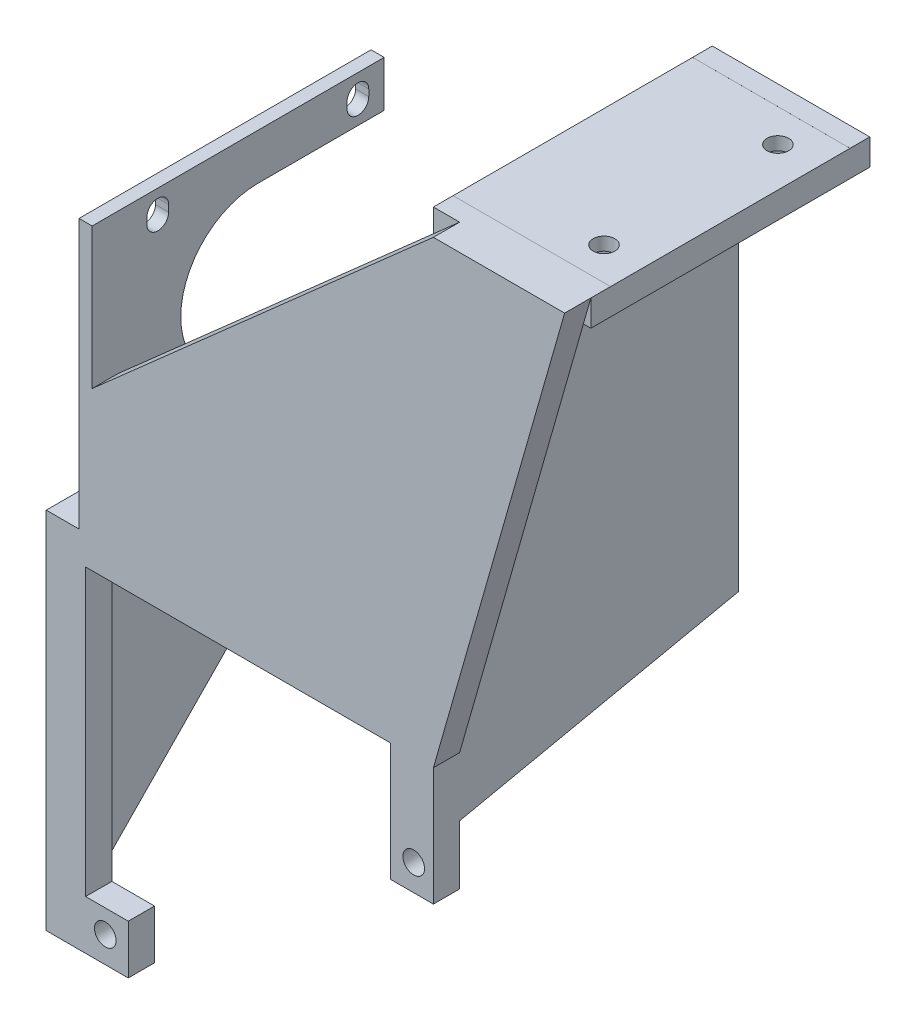
SolidWorks part; units mm, degrees
ref_plane "Front Plane" through (0, 0, 0) normal (0, 0, 1) x (1, 0, 0)
ref_plane "Top Plane" through (0, 0, 0) normal (0, 1, 0) x (1, 0, 0)
ref_plane "Right Plane" through (0, 0, 0) normal (1, 0, 0) x (0, 0, -1)
sketch "Sketch1" plane through (0, 0, 0) normal (1, 0, 0) x (0, 0, -1)
  line L1 (0, 0) -> (13, 0)
  line L2 (0, 0) -> (0, -16)
  line L3 (0, -16) -> (13, -16)
  line L4 (13, 0) -> (13, -16)
  dimension "D1" = 13
  dimension "D2" = 16
extrude "Boss-Extrude1" add sketch "Sketch1" along normal blind 4
sketch "Sketch2" plane through (4, 0, 0) normal (1, 0, 0) x (0, 0, -1)
  line L0 (13, 0) -> (0, 0) construction
  line L1 (0, -16) -> (13, -16) construction
  line L2 (13, -16) -> (13, 0) construction
  line L3 (0, 0) -> (0, -16) construction
  circle A0 centre (6.5, -4) radius 1.65
  circle A1 centre (6.5, -12) radius 1.65
  dimension "D1" = 3.3
  dimension "D2" = 3.3
  dimension "D3" = 4
  dimension "D4" = 4
  dimension "D5" = 6.5
  dimension "D6" = 6.5
extrude "Cut-Extrude1" cut sketch "Sketch2" against normal blind 10
sketch "Sketch3" plane through (0, -16, 0) normal (0, -1, 0) x (1, 0, 0)
  line L1 (4, 0) -> (0, 0)
  line L2 (4, 0) -> (4, -13)
  line L3 (4, -13) -> (0, -13)
  line L4 (0, 0) -> (0, -13)
extrude "Boss-Extrude2" add sketch "Sketch3" along normal blind 4
sketch "Sketch4" plane through (4, 0, 0) normal (1, 0, 0) x (0, 0, -1)
  line L0 (13, -20) -> (13, 0) construction
  line L1 (0, -20) -> (13, -20)
  line L2 (0, -20) -> (0, -16)
  line L3 (0, -16) -> (13, -16)
  line L4 (13, -20) -> (13, -16)
  dimension "D1" = 4
extrude "Boss-Extrude3" add sketch "Sketch4" along normal blind 60
sketch "Sketch6" plane through (0, -16, 0) normal (0, 1, 0) x (1, 0, 0)
  line L0 (64, 0) -> (4, 0) construction
  line L1 (64, 13) -> (60, 13)
  line L2 (64, 13) -> (64, -21)
  line L3 (64, -21) -> (60, -21)
  line L4 (60, 13) -> (60, -21)
  line L7 (64, 13) -> (60, 13)
  line L8 (64, 13) -> (64, 34)
  line L9 (64, 34) -> (60, 34)
  line L10 (60, 13) -> (60, 34)
  line M2 (4, 0) -> (64, 0)
  line M3 (64, 0) -> (64, 13)
  line M4 (64, 13) -> (4, 13)
  dimension "D1" = 4
  dimension "D2" = 21
  dimension "D3" = 21
extrude "Boss-Extrude4" add sketch "Sketch6" along normal blind 28 contours L4 L3 L2 M2 | L10 L8 L9 M4 | L4 M4 M2 M3
sketch "Sketch12" plane through (0, 0, -34) normal (0, 0, -1) x (-1, 0, 0)
  line L1 (-60, -16) -> (-64, -16)
  line L2 (-60, -16) -> (-60, 12)
  line L3 (-60, 12) -> (-64, 12)
  line L4 (-64, -16) -> (-64, 12)
extrude "Boss-Extrude8" add sketch "Sketch12" along normal blind 1.65
sketch "Sketch13" plane through (0, 0, 21) normal (0, 0, 1) x (1, 0, 0)
  line L1 (60, 12) -> (64, 12)
  line L2 (60, 12) -> (60, -16)
  line L3 (60, -16) -> (64, -16)
  line L4 (64, 12) -> (64, -16)
extrude "Boss-Extrude9" add sketch "Sketch13" along normal blind 1.65
sketch "Sketch14" plane through (0, 12, 0) normal (0, 1, 0) x (1, 0, 0)
  line L0 (64, 35.65) -> (64, -22.65) construction
  line L1 (64, 24.35) -> (60, 24.35)
  line L2 (64, 24.35) -> (64, -11.5284)
  line L3 (64, -11.5284) -> (60, -11.5284)
  line L4 (60, 24.35) -> (60, -11.5284)
  line L5 (60, 35.65) -> (60, -22.65) construction
  line L6 (64, -22.65) -> (60, -22.65) construction
  line L7 (60, 35.65) -> (64, 35.65) construction
  point P10 (62, -22.65)
  dimension "D1" = 11.3
  dimension "D2" = 11.3
extrude "Cut-Extrude5" cut sketch "Sketch14" against normal blind 24
sketch "Sketch15" plane through (64, 0, 0) normal (1, 0, 0) x (0, 0, -1)
  line L0 (-11.5284, 12) -> (-22.65, 12) construction
  line L1 (35.65, 12) -> (24.35, 12) construction
  line L2 (-22.65, -16) -> (-22.65, 12) construction
  line L3 (35.65, 12) -> (35.65, -16) construction
  circle A0 centre (-17, -11.5) radius 1.65
  circle A1 centre (30, -11.5) radius 1.65
  dimension "D1" = 3.3
  dimension "D2" = 3.3
  dimension "D3" = 23.5
  dimension "D4" = 23.5
  dimension "D5" = 5.65
  dimension "D6" = 5.65
extrude "Cut-Extrude6" cut sketch "Sketch15" against normal blind 24
sketch "Sketch16" plane through (0, 12, 0) normal (0, 1, 0) x (1, 0, 0)
  line L1 (60, -22.65) -> (64, -22.65)
  line L2 (60, -22.65) -> (60, -11.5284)
  line L3 (60, -11.5284) -> (64, -11.5284)
  line L4 (64, -22.65) -> (64, -11.5284)
  line L5 (60, 24.35) -> (64, 24.35)
  line L6 (60, 24.35) -> (60, 35.65)
  line L7 (60, 35.65) -> (64, 35.65)
  line L8 (64, 24.35) -> (64, 35.65)
extrude "Boss-Extrude10" add sketch "Sketch16" along normal blind 29.15
sketch "Sketch17" plane through (64, 0, 0) normal (1, 0, 0) x (0, 0, -1)
  line L0 (-22.65, -16) -> (-22.65, 41.15) construction
  line L1 (35.65, 41.15) -> (35.65, -16) construction
  line L2 (-22.65, 41.15) -> (-11.5284, 41.15) construction
  line L3 (24.35, 41.15) -> (35.65, 41.15) construction
  circle A0 centre (-17, 35.5) radius 1.65
  circle A1 centre (30, 35.5) radius 1.65
  dimension "D1" = 3.3
  dimension "D2" = 3.3
  dimension "D4" = 5.65
  dimension "D3" = 5.65
  dimension "D5" = 5.65
  dimension "D6" = 5.65
extrude "Cut-Extrude8" cut sketch "Sketch17" against normal blind 29.15
sketch "Sketch18" plane through (64, 0, 0) normal (1, 0, 0) x (0, 0, -1)
  line L1 (-22.65, -16) -> (13, -16)
  line L2 (-22.65, -16) -> (-22.65, -20)
  line L3 (-22.65, -20) -> (13, -20)
  line L4 (13, -16) -> (13, -20)
  line L5 (0, -20) -> (35.65, -20)
  line L6 (0, -20) -> (0, -16)
  line L7 (0, -16) -> (35.65, -16)
  line L8 (35.65, -20) -> (35.65, -16)
  line M9 (-22.65, -16) -> (0, -16)
  line M10 (0, -16) -> (0, -20)
  line M11 (0, -20) -> (13, -20)
  line M12 (13, -20) -> (13, -16)
  line M13 (13, -16) -> (35.65, -16)
extrude "Boss-Extrude11" add sketch "Sketch18" against normal blind 4 contours L2 L3 M10 M9 | L5 L8 M13 M12 | L1 M10 M11 M12
sketch "Sketch19" plane through (0, 0, -13) normal (0, 0, -1) x (-1, 0, 0)
  line L1 (0, -20) -> (-4, -20)
  line L2 (0, -20) -> (0, 0)
  line L3 (0, 0) -> (-4, 0)
  line L4 (-4, -20) -> (-4, 0)
extrude "Boss-Extrude12" add sketch "Sketch19" along normal blind 40
sketch "Sketch20" plane through (0, 0, 0) normal (-1, 0, 0) x (0, 0, 1)
  line L0 (-53, 0) -> (0, 0) construction
  line L1 (-53, -20) -> (-53, 0) construction
  circle A0 centre (-46.5, -4) radius 1.65
  circle A1 centre (-46.5, -12) radius 1.65
  dimension "D1" = 3.3
  dimension "D2" = 3.3
  dimension "D3" = 4
  dimension "D4" = 8
  dimension "D5" = 6.5
  dimension "D6" = 6.5
extrude "Cut-Extrude9" cut sketch "Sketch20" against normal blind 40
sketch "Sketch21" plane through (0, -16, 0) normal (0, 1, 0) x (1, 0, 0)
  line L0 (4, 53) -> (4, 13) construction
  line L1 (28, 21.75) -> (24, 21.75)
  line L2 (28, 21.75) -> (28, -8.75)
  line L3 (28, -8.75) -> (24, -8.75)
  line L4 (24, 21.75) -> (24, -8.75)
  line L5 (60, 13) -> (4, 13) construction
  line L6 (60, 0) -> (4, 0) construction
  dimension "D1" = 20
  dimension "D2" = 4
  dimension "D3" = 8.75
  dimension "D4" = 8.75
extrude "Boss-Extrude13" add sketch "Sketch21" along normal blind 38.5
sketch "Sketch23" plane through (0, 22.5, 0) normal (0, 1, 0) x (1, 0, 0)
  line L1 (24, 21.75) -> (28, 21.75)
  line L2 (24, 21.75) -> (24, 25.75)
  line L3 (24, 25.75) -> (28, 25.75)
  line L4 (28, 21.75) -> (28, 25.75)
  line L6 (24, 21.75) -> (24, -8.75) construction
  line L7 (28, -8.75) -> (28, 21.75) construction
  line L8 (24, -8.75) -> (28, -8.75)
  line L9 (24, -8.75) -> (24, -12.75)
  line L10 (24, -12.75) -> (28, -12.75)
  line L11 (28, -8.75) -> (28, -12.75)
  dimension "D1" = 4
  dimension "D2" = 4
  dimension "D3" = 4
  dimension "D4" = 0
extrude "Boss-Extrude14" add sketch "Sketch23" against normal blind 38.5
sketch "Sketch24" plane through (0, 22.5, 0) normal (0, 1, 0) x (1, 0, 0)
  line L1 (28, 25.75) -> (24, 25.75)
  line L2 (28, 25.75) -> (28, -12.75)
  line L3 (28, -12.75) -> (24, -12.75)
  line L4 (24, 25.75) -> (24, -12.75)
extrude "Boss-Extrude15" add sketch "Sketch24" along normal blind 3
sketch "Sketch25" plane through (28, 0, 0) normal (1, 0, 0) x (0, 0, -1)
  line L0 (25.75, -16) -> (25.75, 25.5) construction
  line L1 (25.75, -13) -> (-12.75, -13)
  line L2 (25.75, -13) -> (25.75, -20)
  line L3 (25.75, -20) -> (-12.75, -20)
  line L4 (-12.75, -13) -> (-12.75, -20)
  line L5 (13, -16) -> (25.75, -16) construction
  line L6 (-12.75, -16) -> (0, -16) construction
  line L7 (-12.75, -16) -> (-12.75, 25.5) construction
  dimension "D1" = 3
  dimension "D2" = 4
  dimension "D3" = 0
sketch "Sketch27" plane through (0, -20, 0) normal (0, -1, 0) x (1, 0, 0)
  line L1 (64, 22.65) -> (60, 22.65)
  line L2 (64, 22.65) -> (64, -35.65)
  line L3 (64, -35.65) -> (60, -35.65)
  line L4 (60, 22.65) -> (60, -35.65)
extrude "Cut-Extrude10" cut sketch "Sketch27" against normal blind 100
sketch "Sketch29" plane through (28, 0, 0) normal (1, 0, 0) x (0, 0, -1)
  line L2 (-12.75, -13) -> (25.75, -13)
  line L3 (-12.75, -13) -> (-12.75, -20)
  line L4 (-12.75, -20) -> (25.75, -20)
  line L5 (25.75, -13) -> (25.75, -20)
extrude "Boss-Extrude16" add sketch "Sketch29" along normal blind 40 and the other way blind 28
sketch "Sketch30" plane through (24, 0, 0) normal (-1, 0, 0) x (0, 0, 1)
  line L0 (12.75, -13) -> (12.75, 25.5) construction
  line L1 (-25.75, 25.5) -> (12.75, 25.5) construction
  line L2 (-25.75, -13) -> (12.75, -13) construction
  line L3 (-25.75, -13) -> (-25.75, 25.5) construction
  circle A0 centre (8.75, 21.5) radius 1.65
  circle A1 centre (8.75, -9) radius 1.65
  circle A2 centre (-21.75, 21.5) radius 1.65
  circle A3 centre (-21.75, -9) radius 1.65
  dimension "D1" = 3.3
  dimension "D4" = 3.3
  dimension "D7" = 3.3
  dimension "D12" = 3.3
  dimension "D2" = 4
  dimension "D3" = 4
  dimension "D5" = 4
  dimension "D6" = 4
  dimension "D8" = 4
  dimension "D9" = 4
  dimension "D10" = 4
  dimension "D11" = 4
extrude "Cut-Extrude11" cut sketch "Sketch30" against normal blind 40
sketch "Sketch31" plane through (0, 25.5, 0) normal (0, 1, 0) x (1, 0, 0)
  line L0 (28, -12.75) -> (28, 25.75) construction
  line L1 (28, 17.75) -> (24, 17.75)
  line L2 (28, 17.75) -> (28, -4.75)
  line L3 (28, -4.75) -> (24, -4.75)
  line L4 (24, 17.75) -> (24, -4.75)
  line L5 (24, 25.75) -> (24, -12.75) construction
  line L6 (24, -12.75) -> (28, -12.75) construction
  dimension "D1" = 8
  dimension "D2" = 8
extrude "Cut-Extrude12" cut sketch "Sketch31" against normal blind 38.5
sketch "Sketch32" plane through (68, 0, 0) normal (1, 0, 0) x (0, 0, -1)
  line L0 (25.75, -20) -> (25.75, -13) construction
  line L1 (-12.75, -13) -> (25.75, -13)
  line L2 (-12.75, -13) -> (-12.75, -15.5)
  line L3 (-12.75, -15.5) -> (25.75, -15.5)
  line L4 (25.75, -13) -> (25.75, -15.5)
  dimension "D1" = 2.5
extrude "Cut-Extrude13" cut sketch "Sketch32" against normal blind 40
sketch "Sketch33" plane through (0, 25.5, 0) normal (0, 1, 0) x (1, 0, 0)
  line L1 (24, -12.75) -> (28, -12.75)
  line L2 (24, -12.75) -> (24, -4.75)
  line L3 (24, -4.75) -> (28, -4.75)
  line L4 (28, -12.75) -> (28, -4.75)
  line L5 (24, 17.75) -> (28, 17.75)
  line L6 (24, 17.75) -> (24, 25.75)
  line L7 (24, 25.75) -> (28, 25.75)
  line L8 (28, 17.75) -> (28, 25.75)
extrude "Boss-Extrude17" add sketch "Sketch33" against normal blind 8
sketch "Sketch34" plane through (28, 0, 0) normal (1, 0, 0) x (0, 0, -1)
  line L0 (-12.75, 25.5) -> (-4.75, 25.5) construction
  line L1 (-12.75, -15.5) -> (-12.75, 25.5) construction
  line L2 (25.75, -15.5) -> (25.75, 25.5) construction
  line L3 (17.75, 25.5) -> (25.75, 25.5) construction
  circle A0 centre (-8.75, 21.5) radius 1.65
  circle A1 centre (21.75, 21.5) radius 1.65
  dimension "D1" = 3.3
  dimension "D2" = 3.3
  dimension "D3" = 4
  dimension "D4" = 4
  dimension "D5" = 4
  dimension "D6" = 4
extrude "Cut-Extrude14" cut sketch "Sketch34" against normal blind 8
sketch "Sketch35" plane through (0, -13, 0) normal (0, 1, 0) x (1, 0, 0)
  line L0 (0, -12.75) -> (24, -12.75) construction
  line L1 (10, -12.75) -> (14, -12.75)
  line L2 (10, -12.75) -> (10, 30.75)
  line L3 (10, 30.75) -> (14, 30.75)
  line L4 (14, -12.75) -> (14, 30.75)
  line L5 (24, 25.75) -> (24, 17.75) construction
  line L6 (4, 25.75) -> (24, 25.75) construction
  dimension "D1" = 10
  dimension "D2" = 4
  dimension "D3" = 5
extrude "Boss-Extrude18" add sketch "Sketch35" along normal blind 13
sketch "Sketch36" plane through (0, -20, 0) normal (0, -1, 0) x (1, 0, 0)
  line L1 (0, 12.75) -> (68, 12.75) construction
  line L2 (0, 12.75) -> (10, 12.75)
  line L3 (0, 12.75) -> (0, -67.25)
  line L4 (0, -67.25) -> (10, -67.25)
  line L5 (10, 12.75) -> (10, -67.25)
  line L6 (4, -53) -> (4, -25.75) construction
  dimension "D1" = 10
  dimension "D2" = 80
  dimension "D3" = 4
extrude "Cut-Extrude15" cut sketch "Sketch36" against normal up to vertex
sketch "Sketch37" plane through (10, 0, 0) normal (-1, 0, 0) x (0, 0, 1)
  line L1 (-30.75, -13) -> (-25.75, -13)
  line L2 (-30.75, -13) -> (-30.75, -20)
  line L3 (-30.75, -20) -> (-25.75, -20)
  line L4 (-25.75, -13) -> (-25.75, -20)
extrude "Boss-Extrude19" add sketch "Sketch37" against normal blind 4
sketch "Sketch41" plane through (14, 0, 0) normal (1, 0, 0) x (0, 0, -1)
  line L1 (25.75, -20) -> (38.75, -20)
  line L2 (25.75, -20) -> (25.75, 0)
  line L3 (25.75, 0) -> (38.75, 0)
  line L4 (38.75, -20) -> (38.75, 0)
  dimension "D1" = 13
  dimension "D2" = 20
extrude "Boss-Extrude20" add sketch "Sketch41" against normal blind 4
sketch "Sketch42" plane through (10, 0, 0) normal (-1, 0, 0) x (0, 0, 1)
  line L0 (-38.75, 0) -> (12.75, 0) construction
  line L1 (-38.75, -20) -> (-38.75, 0) construction
  circle A0 centre (-32.25, -4) radius 1.65
  circle A1 centre (-32.25, -12) radius 1.65
  dimension "D1" = 3.3
  dimension "D2" = 3.3
  dimension "D3" = 4
  dimension "D4" = 6.5
  dimension "D5" = 8
  dimension "D6" = 6.5
extrude "Cut-Extrude18" cut sketch "Sketch42" against normal blind 4
sketch "Sketch43" plane through (0, 0, 0) normal (0, 1, 0) x (1, 0, 0)
  line L0 (10, 38.75) -> (10, -12.75) construction
  line L1 (14, -12.75) -> (10, -12.75)
  line L2 (14, -12.75) -> (14, 25.75)
  line L3 (14, 25.75) -> (10, 25.75)
  line L4 (10, -12.75) -> (10, 25.75)
  line L5 (10, 38.75) -> (14, 38.75) construction
  dimension "D1" = 13
extrude "Cut-Extrude19" cut sketch "Sketch43" against normal blind 10
sketch "Sketch44" plane through (28, 0, 0) normal (1, 0, 0) x (0, 0, -1)
  line L0 (-4.75, -13) -> (-4.75, 25.5) construction
  line L1 (-12.75, -15.5) -> (-4.75, -15.5)
  line L2 (-12.75, -15.5) -> (-12.75, -6.5)
  line L3 (-12.75, -6.5) -> (-4.75, -6.5)
  line L4 (-4.75, -15.5) -> (-4.75, -6.5)
  line L5 (17.75, -13) -> (17.75, 25.5) construction
  line L6 (25.75, -15.5) -> (17.75, -15.5)
  line L7 (25.75, -15.5) -> (25.75, -6.5)
  line L8 (25.75, -6.5) -> (17.75, -6.5)
  line L9 (17.75, -15.5) -> (17.75, -6.5)
  dimension "D1" = 9
  dimension "D2" = 9
extrude "Boss-Extrude21" add sketch "Sketch44" against normal blind 4
sketch "Sketch45" plane through (24, 0, 0) normal (-1, 0, 0) x (0, 0, 1)
  line L0 (4.75, -13) -> (12.75, -13) construction
  line L1 (-25.75, -13) -> (-17.75, -13) construction
  line L2 (-25.75, -13) -> (-25.75, 25.5) construction
  line L3 (12.75, -13) -> (12.75, 25.5) construction
  circle A0 centre (-21.75, -7) radius 1.65
  circle A1 centre (8.75, -7) radius 1.65
  dimension "D1" = 3.3
  dimension "D2" = 3.3
  dimension "D3" = 6
  dimension "D4" = 6
  dimension "D5" = 4
  dimension "D6" = 4
extrude "Cut-Extrude20" cut sketch "Sketch45" against normal blind 4
sketch "Sketch46" plane through (0, -15.5, 0) normal (0, 1, 0) x (1, 0, 0)
  line L0 (68, -12.75) -> (68, 25.75) construction
  line L1 (64, 18.2859) -> (67, 20.0179)
  line L2 (67, 20.0179) -> (67, 23.4821)
  line L3 (67, 23.4821) -> (64, 25.2141)
  line L4 (64, 25.2141) -> (61, 23.4821)
  line L5 (61, 23.4821) -> (61, 20.0179)
  line L6 (61, 20.0179) -> (64, 18.2859)
  line L7 (64, -12.2141) -> (67, -10.4821)
  line L8 (67, -10.4821) -> (67, -7.0179)
  line L9 (67, -7.0179) -> (64, -5.2859)
  line L10 (64, -5.2859) -> (61, -7.0179)
  line L11 (61, -7.0179) -> (61, -10.4821)
  line L12 (61, -10.4821) -> (64, -12.2141)
  line L13 (28, 25.75) -> (68, 25.75) construction
  line L14 (28, -12.75) -> (68, -12.75) construction
  circle A0 centre (64, 21.75) radius 3 construction
  circle A1 centre (64, -8.75) radius 3 construction
  dimension "D3" = 6
  dimension "D7" = 6
  dimension "D1" = 4
  dimension "D2" = 4
  dimension "D4" = 1
  dimension "D5" = 4
  dimension "D6" = 4
  dimension "D8" = 1
extrude "Cut-Extrude21" cut sketch "Sketch46" against normal blind 3
sketch "Sketch49" plane through (0, -15.5, 0) normal (0, 1, 0) x (1, 0, 0)
  line L0 (68, -12.75) -> (68, 25.75) construction
  line L1 (28, 25.75) -> (68, 25.75) construction
  line L2 (28, -12.75) -> (68, -12.75) construction
  circle A0 centre (64, 21.75) radius 1.65
  circle A1 centre (64, -8.75) radius 1.65
  dimension "D1" = 3.3
  dimension "D2" = 3.3
  dimension "D3" = 4
  dimension "D4" = 4
  dimension "D5" = 4
  dimension "D6" = 4
extrude "Cut-Extrude22" cut sketch "Sketch49" against normal blind 5
ref_plane "Plane1" through (10, -10, -25.75) normal (0, 0, 1) x (1, 0, 0)
sketch "Sketch54" plane through (0, -10, 0) normal (0, 1, 0) x (1, 0, 0)
  line L0 (10, -12.75) -> (14, -12.75) construction
  line L1 (10, 25.75) -> (11, 25.75)
  line L2 (10, 25.75) -> (10, -12.75)
  line L3 (10, -12.75) -> (11, -12.75)
  line L4 (11, 25.75) -> (11, -12.75)
  dimension "D1" = 1
  dimension "D2" = 0
extrude "Cut-Extrude24" cut sketch "Sketch54" against normal blind 50
sketch "Sketch55" plane through (24, 0, 0) normal (-1, 0, 0) x (0, 0, 1)
  line L0 (4.75, -13) -> (4.75, 25.5) construction
  line L1 (12.75, -13) -> (4.75, -13)
  line L2 (12.75, -13) -> (12.75, -3)
  line L3 (12.75, -3) -> (4.75, -3)
  line L4 (4.75, -13) -> (4.75, -3)
  line L5 (-25.75, -13) -> (-25.75, 25.5) construction
  line L6 (-17.75, -13) -> (-25.75, -13)
  line L7 (-17.75, -13) -> (-17.75, -3)
  line L8 (-17.75, -3) -> (-25.75, -3)
  line L9 (-25.75, -13) -> (-25.75, -3)
  dimension "D1" = 10
  dimension "D2" = 10
extrude "Boss-Extrude22" add sketch "Sketch55" against normal blind 4
sketch "Sketch56" plane through (24, 0, 0) normal (-1, 0, 0) x (0, 0, 1)
  line L0 (-17.75, -13) -> (-17.75, 25.5) construction
  line L1 (4.75, -13) -> (4.75, 25.5) construction
  circle A0 centre (-21.75, -9) radius 1.65
  circle A1 centre (8.75, -9) radius 1.65
  circle A2 centre (-21.75, 21.5) radius 1.65 construction
  circle A3 centre (8.75, 21.5) radius 1.65 construction
  dimension "D3" = 3.3
  dimension "D4" = 3.3
  dimension "D1" = 30.5
  dimension "D2" = 30.5
  dimension "D5" = 4
  dimension "D6" = 4
extrude "Cut-Extrude25" cut sketch "Sketch56" against normal blind 4
sketch "Sketch57" plane through (0, -13, 0) normal (0, 1, 0) x (1, 0, 0)
  line L1 (24, -12.75) -> (-1, -12.75)
  line L2 (24, -12.75) -> (24, 57.25)
  line L3 (24, 57.25) -> (-1, 57.25)
  line L4 (-1, -12.75) -> (-1, 57.25)
  dimension "D1" = 70
  dimension "D2" = 25
extrude "Cut-Extrude26" cut sketch "Sketch57" against normal blind 10 and the other way blind 15
sketch "Sketch58" plane through (0, -20, 0) normal (0, -1, 0) x (1, 0, 0)
  line L0 (28, -25.75) -> (28, 12.75) construction
  line L1 (28, -25.75) -> (75.5, -25.75)
  line L2 (28, -25.75) -> (28, 12.75)
  line L3 (28, 12.75) -> (75.5, 12.75)
  line L4 (75.5, -25.75) -> (75.5, 12.75)
  line L5 (24, -25.75) -> (68, -25.75) construction
  dimension "D1" = 38.5
  dimension "D2" = 47.5
extrude "Boss-Extrude24" add sketch "Sketch58" against normal blind 4.5
sketch "Sketch59" plane through (0, -20, 0) normal (0, -1, 0) x (1, 0, 0)
  line L0 (24, -25.75) -> (75.5, -25.75) construction
  line L1 (75.5, 12.75) -> (76, 12.75)
  line L2 (75.5, 12.75) -> (75.5, -25.75)
  line L3 (75.5, -25.75) -> (76, -25.75)
  line L4 (76, 12.75) -> (76, -25.75)
  dimension "D1" = 0
  dimension "D2" = 0.5
extrude "Boss-Extrude25" add sketch "Sketch59" against normal blind 4.5
sketch "Sketch60" plane through (0, -20, 0) normal (0, -1, 0) x (1, 0, 0)
  line L0 (24, -25.75) -> (76, -25.75) construction
  line L1 (76, 12.75) -> (80, 12.75)
  line L2 (76, 12.75) -> (76, -25.75)
  line L3 (76, -25.75) -> (80, -25.75)
  line L4 (80, 12.75) -> (80, -25.75)
  dimension "D1" = 0
  dimension "D2" = 4
extrude "Boss-Extrude26" add sketch "Sketch60" against normal blind 69.5
sketch "Sketch61" plane through (80, 0, 0) normal (1, 0, 0) x (0, 0, -1)
  line L0 (-12.75, 49.5) -> (-12.75, -20) construction
  line L1 (25.75, 49.5) -> (-12.75, 49.5)
  line L2 (25.75, 49.5) -> (25.75, 47.0423)
  line L3 (25.75, 47.0423) -> (-12.75, 47.0423)
  line L4 (-12.75, 49.5) -> (-12.75, 47.0423)
extrude "Boss-Extrude27" add sketch "Sketch61" along normal blind 20
sketch "Sketch62" plane through (76, 0, 0) normal (-1, 0, 0) x (0, 0, 1)
  line L0 (12.75, 49.5) -> (12.75, -15.5) construction
  line L1 (12.75, 28) -> (-25.75, 28)
  line L2 (12.75, 28) -> (12.75, 30)
  line L3 (12.75, 30) -> (-25.75, 30)
  line L4 (-25.75, 28) -> (-25.75, 30)
  line L5 (-25.75, 49.5) -> (-25.75, -15.5) construction
  line L6 (-25.75, -15.5) -> (12.75, -15.5) construction
  dimension "D1" = 43.5
  dimension "D2" = 2
extrude "Boss-Extrude31" add sketch "Sketch62" along normal blind 29.5
sketch "Sketch64" plane through (0, 30, 0) normal (0, 1, 0) x (1, 0, 0)
  line L0 (46.5, -12.75) -> (46.5, 25.75) construction
  line L1 (46.5, 0) -> (50.5, 0)
  line L2 (46.5, 0) -> (46.5, 13)
  line L3 (46.5, 13) -> (50.5, 13)
  line L4 (50.5, 0) -> (50.5, 13)
  line L5 (46.5, -12.75) -> (76, -12.75) construction
  dimension "D1" = 12.75
  dimension "D2" = 13
  dimension "D3" = 4
extrude "Boss-Extrude32" add sketch "Sketch64" along normal blind 16
sketch "Sketch65" plane through (46.5, 0, 0) normal (-1, 0, 0) x (0, 0, 1)
  line L0 (-13, 46) -> (0, 46) construction
  line L1 (-13, 46) -> (-13, 30) construction
  line L2 (0, 46) -> (0, 30) construction
  circle A0 centre (-6.5, 34) radius 1.65
  circle A1 centre (-6.5, 42) radius 1.65
  dimension "D3" = 3.3
  dimension "D6" = 3.3
  dimension "D1" = 4
  dimension "D2" = 6.5
  dimension "D4" = 6.5
  dimension "D5" = 8
extrude "Cut-Extrude27" cut sketch "Sketch65" against normal blind 16
sketch "Sketch66" plane through (0, 0, -25.75) normal (0, 0, -1) x (-1, 0, 0)
  line L1 (-76, 49.5) -> (-100, 49.5)
  line L2 (-76, 49.5) -> (-76, 50)
  line L3 (-76, 50) -> (-100, 50)
  line L4 (-100, 49.5) -> (-100, 50)
  dimension "D1" = 0.5
extrude "Boss-Extrude33" add sketch "Sketch66" against normal blind 38.5
sketch "Sketch67" plane through (0, 47.0423, 0) normal (0, -1, 0) x (1, 0, 0)
  line L1 (80, -25.75) -> (100, -25.75)
  line L2 (80, -25.75) -> (80, 12.75)
  line L3 (80, 12.75) -> (100, 12.75)
  line L4 (100, -25.75) -> (100, 12.75)
sketch "Sketch69" plane through (0, 47.0423, 0) normal (0, -1, 0) x (1, 0, 0)
  line L1 (80, -25.75) -> (100, -25.75)
  line L2 (80, -25.75) -> (80, 12.75)
  line L3 (80, 12.75) -> (100, 12.75)
  line L4 (100, -25.75) -> (100, 12.75)
extrude "Boss-Extrude34" add sketch "Sketch69" along normal blind 1.04
sketch "Sketch70" plane through (0, 46.0023, 0) normal (0, -1, 0) x (1, 0, 0)
  line L0 (100, -25.75) -> (100, 12.75) construction
  line L1 (80, 12.75) -> (100, 12.75) construction
  line L2 (80, -25.75) -> (100, -25.75) construction
  circle A0 centre (94, 6.75) radius 1.65
  circle A1 centre (94, -19.75) radius 1.65
  dimension "D5" = 3.3
  dimension "D6" = 3.3
  dimension "D1" = 6
  dimension "D2" = 6
  dimension "D3" = 6
  dimension "D4" = 6
extrude "Cut-Extrude29" cut sketch "Sketch70" against normal blind 10
sketch "Sketch72" plane through (0, -20, 0) normal (0, -1, 0) x (1, 0, 0)
  line L0 (24, -25.75) -> (80, -25.75) construction
  line L1 (24, 12.75) -> (26, 12.75)
  line L2 (24, 12.75) -> (24, -25.75)
  line L3 (24, -25.75) -> (26, -25.75)
  line L4 (26, 12.75) -> (26, -25.75)
  dimension "D1" = 2
extrude "Cut-Extrude31" cut sketch "Sketch72" against normal blind 60
sketch "Sketch73" plane through (26, 0, 0) normal (-1, 0, 0) x (0, 0, 1)
  line L0 (-25.75, 25.5) -> (-17.75, 25.5) construction
  line L1 (4.75, -13) -> (-17.75, -13)
  line L2 (4.75, -13) -> (4.75, 25.5)
  line L3 (4.75, 25.5) -> (-17.75, 25.5)
  line L4 (-17.75, -13) -> (-17.75, 25.5)
  line L5 (-17.75, 25.5) -> (-17.75, -13) construction
extrude "Boss-Extrude35" add sketch "Sketch73" against normal blind 2
sketch "Sketch74" plane through (26, 0, 0) normal (-1, 0, 0) x (0, 0, 1)
  line L0 (-25.75, 25.5) -> (12.75, 25.5) construction
  line L1 (12.75, 25.5) -> (12.75, -20) construction
  circle A0 centre (-6.5, 6.25) radius 11.25
  dimension "D3" = 22.5
  dimension "D1" = 19.25
  dimension "D2" = 19.25
extrude "Cut-Extrude32" cut sketch "Sketch74" against normal blind 2
sketch "Sketch75" plane through (26, 0, 0) normal (-1, 0, 0) x (0, 0, 1)
  line L0 (-25.75, 25.5) -> (-25.75, -20) construction
  line L1 (-6.5, 6.25) -> (-25.75, 6.25)
  line L2 (-6.5, 6.25) -> (-6.5, 17.5)
  line L3 (-6.5, 17.5) -> (-25.75, 17.5)
  line L4 (-25.75, 6.25) -> (-25.75, 17.5)
  line L6 (-6.5, 6.25) -> (-25.75, 6.25)
  line L7 (-6.5, 6.25) -> (-6.5, -5)
  line L8 (-6.5, -5) -> (-25.75, -5)
  line L9 (-25.75, 6.25) -> (-25.75, -5)
  dimension "D1" = 11.25
  dimension "D2" = 11.25
sketch "Sketch76" plane through (76, 0, 0) normal (-1, 0, 0) x (0, 0, 1)
  line L0 (12.75, 30) -> (-25.75, 30) construction
  line L1 (12.75, 50) -> (12.75, 30) construction
  line L2 (-25.75, 50) -> (-25.75, 30) construction
  circle A0 centre (2.75, 36) radius 1.65
  circle A1 centre (-15.75, 36) radius 1.65
  dimension "D3" = 3.3
  dimension "D6" = 3.3
  dimension "D1" = 6
  dimension "D2" = 10
  dimension "D4" = 6
  dimension "D5" = 10
extrude "Cut-Extrude34" cut sketch "Sketch76" against normal blind 5
sketch "Sketch77" plane through (0, 0, 12.75) normal (0, 0, 1) x (1, 0, 0)
  line L1 (76, 28) -> (41, 28)
  line L2 (76, 28) -> (76, 58)
  line L3 (76, 58) -> (41, 58)
  line L4 (41, 28) -> (41, 58)
  dimension "D1" = 35
  dimension "D2" = 30
extrude "Cut-Extrude35" cut sketch "Sketch77" against normal blind 1000
sketch "Sketch78" plane through (26, 0, 0) normal (-1, 0, 0) x (0, 0, 1)
  line L0 (-6.5, 6.25) -> (-25.75, 6.25) construction
  line L1 (-25.75, 6.25) -> (-25.75, 17.5) construction
  circle A0 centre (-6.5, 6.75) radius 11.75
  dimension "D2" = 23.5
  dimension "D1" = 0.5
  dimension "D3" = 19.25
extrude "Cut-Extrude36" cut sketch "Sketch78" against normal blind 10
sketch "Sketch79" plane through (26, 0, 0) normal (-1, 0, 0) x (0, 0, 1)
  line L0 (-25.75, -65) -> (-25.75, 45) construction
  line L1 (-6.5, -5) -> (-25.75, -5)
  line L2 (-6.5, -5) -> (-6.5, 18.5)
  line L3 (-6.5, 18.5) -> (-25.75, 18.5)
  line L4 (-25.75, -5) -> (-25.75, 18.5)
  dimension "D1" = 23.5
  dimension "D2" = 0
extrude "Cut-Extrude37" cut sketch "Sketch79" against normal blind 10
sketch "Sketch80" plane through (26, 0, 0) normal (-1, 0, 0) x (0, 0, 1)
  line L0 (-25.75, 25.5) -> (12.75, 25.5) construction
  line L1 (12.75, 25.5) -> (12.75, -20) construction
  line L2 (-25.75, 25.5) -> (-25.75, 18.5) construction
  circle A0 centre (8.75, 22.5) radius 1.65
  circle A1 centre (-21.75, 22.5) radius 1.65
  dimension "D1" = 3.3
  dimension "D4" = 3.3
  dimension "D2" = 3
  dimension "D3" = 4
  dimension "D5" = 3
  dimension "D6" = 4
extrude "Cut-Extrude38" cut sketch "Sketch80" against normal blind 10
sketch "Sketch81" plane through (26, 0, 0) normal (-1, 0, 0) x (0, 0, 1)
  line L0 (-25.75, 25.5) -> (12.75, 25.5) construction
  line L1 (10.4, 21.5) -> (7.1, 21.5)
  line L2 (10.4, 21.5) -> (10.4, 22.5)
  line L3 (10.4, 22.5) -> (7.1, 22.5)
  line L4 (7.1, 21.5) -> (7.1, 22.5)
  line L5 (-20.1, 21.5) -> (-23.4, 21.5)
  line L6 (-20.1, 21.5) -> (-20.1, 22.5)
  line L7 (-20.1, 22.5) -> (-23.4, 22.5)
  line L8 (-23.4, 21.5) -> (-23.4, 22.5)
  line L9 (-25.75, 25.5) -> (-25.75, 18.5) construction
  arc A0 (7.1776, 22) -> (10.3224, 22) centre (8.75, 21.5) ccw construction
  dimension "D1" = 3
  dimension "D2" = 3
  dimension "D3" = 4
  dimension "D4" = 3.3
  dimension "D5" = 2.35
  dimension "D6" = 3.3
  dimension "D7" = 3
  dimension "D8" = 4
extrude "Cut-Extrude39" cut sketch "Sketch81" against normal blind 10
sketch "Sketch82" plane through (0, 46.0023, 0) normal (0, -1, 0) x (1, 0, 0)
  line L0 (100, -25.75) -> (100, 12.75) construction
  line L1 (97, -18.0179) -> (94, -16.2859)
  line L2 (94, -16.2859) -> (91, -18.0179)
  line L3 (91, -18.0179) -> (91, -21.4821)
  line L4 (91, -21.4821) -> (94, -23.2141)
  line L5 (94, -23.2141) -> (97, -21.4821)
  line L6 (97, -21.4821) -> (97, -18.0179)
  line L7 (97, 8.4821) -> (94, 10.2141)
  line L8 (94, 10.2141) -> (91, 8.4821)
  line L9 (91, 8.4821) -> (91, 5.0179)
  line L10 (91, 5.0179) -> (94, 3.2859)
  line L11 (94, 3.2859) -> (97, 5.0179)
  line L12 (97, 5.0179) -> (97, 8.4821)
  circle A0 centre (94, -19.75) radius 3 construction
  circle A1 centre (94, 6.75) radius 3 construction
  dimension "D1" = 6
  dimension "D2" = 6
  dimension "D3" = 3
  dimension "D4" = 3
extrude "Cut-Extrude41" cut sketch "Sketch82" against normal blind 2
sketch "Sketch83" plane through (0, -20, 0) normal (0, -1, 0) x (1, 0, 0)
  line L0 (26, -25.75) -> (80, -25.75) construction
  line L1 (26, -27.75) -> (80, -27.75)
  line L2 (26, -27.75) -> (26, 14.75)
  line L3 (26, 14.75) -> (80, 14.75)
  line L4 (80, -27.75) -> (80, 14.75)
  line L5 (26, 12.75) -> (80, 12.75) construction
  line L6 (26, -25.75) -> (26, 12.75) construction
  line L7 (80, -25.75) -> (80, 12.75) construction
  dimension "D1" = 2
  dimension "D2" = 2
  dimension "D3" = 0
  dimension "D4" = 0
extrude "Boss-Extrude37" add sketch "Sketch83" against normal blind 4.5
sketch "Sketch84" plane through (80, 0, 0) normal (1, 0, 0) x (0, 0, -1)
  line L0 (-12.75, 46.0023) -> (25.75, 46.0023) construction
  line L1 (27.75, -15.5) -> (25.75, -15.5)
  line L2 (27.75, -15.5) -> (27.75, 46.0023)
  line L3 (27.75, 46.0023) -> (25.75, 46.0023)
  line L4 (25.75, -15.5) -> (25.75, 46.0023)
  line L5 (25.75, 46.0023) -> (25.75, -15.5) construction
  line L7 (-12.75, -15.5) -> (-14.75, -15.5)
  line L8 (-12.75, -15.5) -> (-12.75, 46.0023)
  line L9 (-12.75, 46.0023) -> (-14.75, 46.0023)
  line L10 (-14.75, -15.5) -> (-14.75, 46.0023)
  dimension "D1" = 2
extrude "Boss-Extrude38" add sketch "Sketch84" against normal blind 4
sketch "Sketch85" plane through (0, 46.0023, 0) normal (0, -1, 0) x (1, 0, 0)
  line L0 (100, -25.75) -> (100, 12.75) construction
  line L1 (76, -27.75) -> (100, -27.75)
  line L2 (76, -27.75) -> (76, -24.75)
  line L3 (76, -24.75) -> (100, -24.75)
  line L4 (100, -27.75) -> (100, -24.75)
  line L5 (76, 14.75) -> (100, 14.75)
  line L6 (76, 14.75) -> (76, 11.75)
  line L7 (76, 11.75) -> (100, 11.75)
  line L8 (100, 14.75) -> (100, 11.75)
  line L9 (80, -25.75) -> (100, -25.75) construction
  line L10 (80, 12.75) -> (100, 12.75) construction
  dimension "D1" = 0
  dimension "D2" = 0
  dimension "D3" = 1
  dimension "D4" = 1
extrude "Boss-Extrude40" add sketch "Sketch85" against normal blind 4
sketch "Sketch86" plane through (0, 0, 14.75) normal (0, 0, 1) x (1, 0, 0)
  line L1 (76, 50.0023) -> (80, 50.0023)
  line L2 (76, 50.0023) -> (76, -20)
  line L3 (76, -20) -> (80, -20)
  line L4 (80, 50.0023) -> (80, -20)
sketch "Sketch87" plane through (0, 0, 14.75) normal (0, 0, 1) x (1, 0, 0)
  line L0 (80, 50.0023) -> (26, -20)
  line L1 (80, 50.0023) -> (80, -20)
  line L2 (26, -20) -> (80, -20)
extrude "Boss-Extrude41" add sketch "Sketch87" along normal blind 4
sketch "Sketch88" plane through (0, 0, 14.75) normal (0, 0, 1) x (1, 0, 0)
  line L0 (80, -20) -> (100, 50.0023)
  line L1 (100, 50.0023) -> (80, 50.0023)
  line L2 (80, -20) -> (80, 50.0023)
extrude "Boss-Extrude42" add sketch "Sketch88" along normal blind 4
sketch "Sketch89" plane through (26, 0, 0) normal (-1, 0, 0) x (0, 0, 1)
  line L1 (18.75, -20) -> (12.75, -20)
  line L2 (18.75, -20) -> (18.75, 25.5)
  line L3 (18.75, 25.5) -> (12.75, 25.5)
  line L4 (12.75, -20) -> (12.75, 25.5)
extrude "Boss-Extrude43" add sketch "Sketch89" against normal blind 2
sketch "Sketch90" plane through (0, 0, 18.75) normal (0, 0, 1) x (1, 0, 0)
  line L0 (28, -17.4073) -> (80, 50.0023)
  line L1 (80, 50.0023) -> (28, 4.0463)
  line L2 (28, -17.4073) -> (28, 25.5) construction
  line L3 (28, 4.0463) -> (28, -17.4073)
extrude "Boss-Extrude44" add sketch "Sketch90" against normal blind 4
sketch "Sketch91" plane through (26, 0, 0) normal (-1, 0, 0) x (0, 0, 1)
  line L0 (-27.75, -20) -> (18.75, -20) construction
  line L1 (18.75, -20) -> (18.75, 25.5) construction
  circle A0 centre (10.25, -9) radius 1.65
  dimension "D1" = 3.3
  dimension "D3" = 11
  dimension "D5" = 8.5
extrude "Cut-Extrude42" cut sketch "Sketch91" against normal blind 10
sketch "Sketch92" plane through (26, 0, 0) normal (-1, 0, 0) x (0, 0, 1)
  line L0 (-27.75, -20) -> (18.75, -20) construction
  line L1 (18.75, -20) -> (18.75, 25.5) construction
  circle A0 centre (7.25, -9) radius 1.65
  dimension "D1" = 3.3
  dimension "D2" = 11
  dimension "D3" = 11.5
extrude "Cut-Extrude43" cut sketch "Sketch92" against normal blind 10
sketch "Sketch93" plane through (26, 0, 0) normal (-1, 0, 0) x (0, 0, 1)
  line L0 (18.75, -20) -> (18.75, 25.5) construction
  line L1 (10.25, -10.65) -> (7.25, -10.65)
  line L2 (10.25, -10.65) -> (10.25, -7.35)
  line L3 (10.25, -7.35) -> (7.25, -7.35)
  line L4 (7.25, -10.65) -> (7.25, -7.35)
  line L5 (-27.75, -20) -> (18.75, -20) construction
  dimension "D1" = 8.5
  dimension "D2" = 11.5
  dimension "D3" = 9.35
  dimension "D4" = 12.65
extrude "Cut-Extrude44" cut sketch "Sketch93" against normal blind 10
sketch "Sketch95" plane through (26, 0, 0) normal (-1, 0, 0) x (0, 0, 1)
  line L1 (-27.75, -15.5) -> (18.75, -15.5)
  line L2 (-27.75, -15.5) -> (-27.75, -20)
  line L3 (-27.75, -20) -> (18.75, -20)
  line L4 (18.75, -15.5) -> (18.75, -20)
extrude "Boss-Extrude45" add sketch "Sketch95" along normal blind 5
sketch "Sketch96" plane through (0, -20, 0) normal (0, -1, 0) x (1, 0, 0)
  line L0 (21, 18.75) -> (80, 18.75) construction
  line L1 (80, 14.75) -> (72.7, 14.75)
  line L2 (80, 14.75) -> (80, 18.75)
  line L3 (80, 18.75) -> (72.7, 18.75)
  line L4 (72.7, 14.75) -> (72.7, 18.75)
  line L5 (80, -27.75) -> (80, 14.75) construction
  dimension "D1" = 0
  dimension "D2" = 7.3
  dimension "D3" = 4
extrude "Boss-Extrude47" add sketch "Sketch96" along normal blind 18
sketch "Sketch99" plane through (0, 0, 18.75) normal (0, 0, 1) x (1, 0, 0)
  line L0 (21, -20) -> (72.7, -20) construction
  line L1 (80, -38) -> (80, -20) construction
  circle A0 centre (76.35, -34) radius 1.65
  dimension "D3" = 3.3
  dimension "D1" = 14
  dimension "D2" = 3.65
extrude "Cut-Extrude47" cut sketch "Sketch99" against normal blind 18
sketch "Sketch100" plane through (0, -20, 0) normal (0, -1, 0) x (1, 0, 0)
  line L1 (21, 18.75) -> (27, 18.75)
  line L2 (21, 18.75) -> (21, 14.75)
  line L3 (21, 14.75) -> (27, 14.75)
  line L4 (27, 18.75) -> (27, 14.75)
  dimension "D1" = 6
  dimension "D2" = 4
extrude "Boss-Extrude48" add sketch "Sketch100" along normal blind 51
sketch "Sketch101" plane through (27, 0, 0) normal (1, 0, 0) x (0, 0, -1)
  line L0 (-18.75, -71) -> (-18.75, -20) construction
  line L1 (-14.75, -71) -> (-18.75, -71)
  line L2 (-14.75, -71) -> (-14.75, -63.5)
  line L3 (-14.75, -63.5) -> (-18.75, -63.5)
  line L4 (-18.75, -71) -> (-18.75, -63.5)
  dimension "D1" = 7.5
extrude "Boss-Extrude50" add sketch "Sketch101" along normal blind 6.5
sketch "Sketch103" plane through (0, 0, 18.75) normal (0, 0, 1) x (1, 0, 0)
  line L0 (33.5, -63.5) -> (33.5, -71) construction
  line L1 (33.5, -71) -> (21, -71) construction
  circle A0 centre (30, -67) radius 1.65
  dimension "D1" = 3.3
  dimension "D2" = 3.5
  dimension "D3" = 4
extrude "Cut-Extrude48" cut sketch "Sketch103" against normal blind 6.5
sketch "Sketch104" plane through (0, 0, 18.75) normal (0, 0, 1) x (1, 0, 0)
  line L1 (72.7, -20) -> (80, -20)
  line L2 (72.7, -20) -> (72.7, -38)
  line L3 (72.7, -38) -> (80, -38)
  line L4 (80, -20) -> (80, -38)
extrude "Cut-Extrude49" cut sketch "Sketch104" against normal blind 6.5
sketch "Sketch105" plane through (0, -20, 0) normal (0, -1, 0) x (1, 0, 0)
  line L1 (80, 18.75) -> (73.5, 18.75)
  line L2 (80, 18.75) -> (80, 14.75)
  line L3 (80, 14.75) -> (73.5, 14.75)
  line L4 (73.5, 18.75) -> (73.5, 14.75)
  dimension "D1" = 4
  dimension "D2" = 6.5
extrude "Boss-Extrude51" add sketch "Sketch105" along normal blind 18
sketch "Sketch106" plane through (0, 0, 18.75) normal (0, 0, 1) x (1, 0, 0)
  line L0 (80, -38) -> (80, -20) construction
  line L1 (27, -20) -> (73.5, -20) construction
  circle A0 centre (77, -34) radius 1.65
  dimension "D1" = 3.3
  dimension "D2" = 3
  dimension "D3" = 14
extrude "Cut-Extrude50" cut sketch "Sketch106" against normal blind 18
sketch "Sketch107" plane through (80, 0, 0) normal (1, 0, 0) x (0, 0, -1)
  line L0 (-14.75, -29) -> (27.75, -20)
  line L1 (-14.75, -38) -> (-14.75, -20) construction
  line L2 (-14.75, -29) -> (-14.75, -20)
  line L3 (27.75, -20) -> (-14.75, -20)
extrude "Boss-Extrude52" add sketch "Sketch107" against normal blind 4
sketch "Sketch109" plane through (21, 0, 0) normal (-1, 0, 0) x (0, 0, 1)
  line L0 (18.75, -71) -> (18.75, -15.5) construction
  line L1 (14.75, -20) -> (18.75, -20)
  line L2 (14.75, -20) -> (14.75, -63.5)
  line L3 (14.75, -63.5) -> (18.75, -63.5)
  line L4 (18.75, -20) -> (18.75, -63.5)
  dimension "D1" = 43.5
sketch "Sketch110" plane through (21, 0, 0) normal (-1, 0, 0) x (0, 0, 1)
  line L0 (-27.75, -20) -> (14.75, -63.5)
  line L1 (14.75, -20) -> (14.75, -63.5)
  line L2 (-27.75, -20) -> (14.75, -20)
extrude "Boss-Extrude53" add sketch "Sketch110" against normal blind 4
